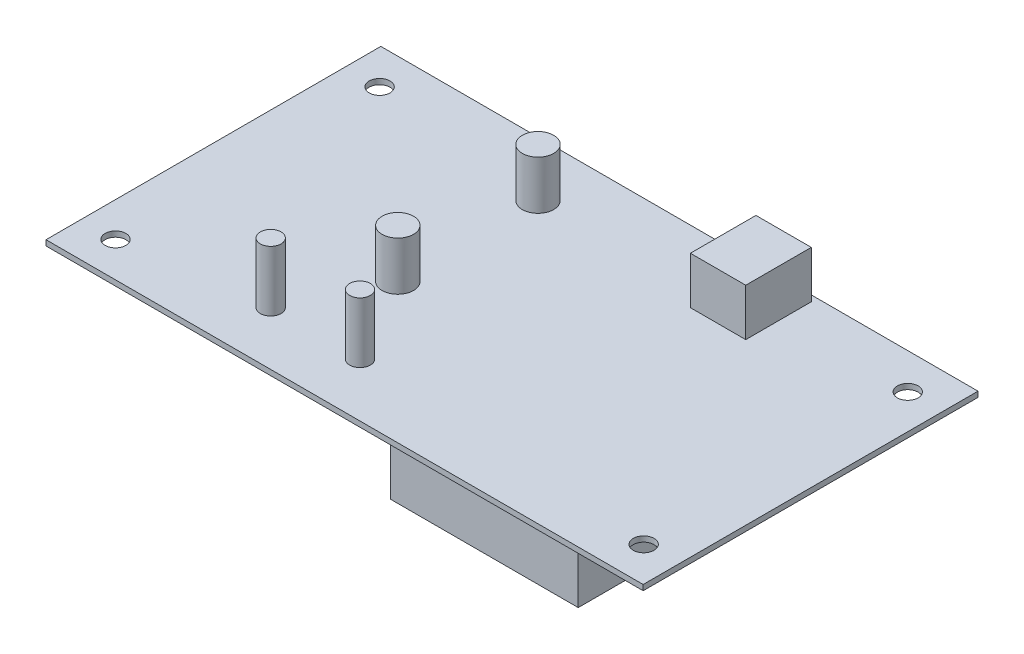
SolidWorks part; units mm, degrees
ref_plane "Front Plane" through (0, 0, 0) normal (0, 0, 1) x (1, 0, 0)
ref_plane "Top Plane" through (0, 0, 0) normal (0, 1, 0) x (1, 0, 0)
ref_plane "Right Plane" through (0, 0, 0) normal (1, 0, 0) x (0, 0, -1)
sketch "Sketch1" plane through (0, 0, 0) normal (0, 1, 0) x (1, 0, 0)
  line L1 (0, 0) -> (169.8625, 0)
  line L2 (0, 0) -> (0, 95.25)
  line L3 (0, 95.25) -> (169.8625, 95.25)
  line L4 (169.8625, 0) -> (169.8625, 95.25)
  dimension "D1" = 169.8625
  dimension "D2" = 95.25
extrude "Boss-Extrude1" add sketch "Sketch1" along normal blind 1.5494
sketch "Sketch2" plane through (0, 1.5494, 0) normal (0, 1, 0) x (1, 0, 0)
  line L0 (169.8625, 0) -> (169.8625, 95.25) construction
  line L1 (108.3945, 93.5482) -> (124.1425, 93.5482)
  line L2 (108.3945, 93.5482) -> (108.3945, 74.9046)
  line L3 (108.3945, 74.9046) -> (124.1425, 74.9046)
  line L4 (124.1425, 93.5482) -> (124.1425, 74.9046)
  line L5 (169.8625, 95.25) -> (0, 95.25) construction
  dimension "D1" = 15.748
  dimension "D2" = 18.6436
  dimension "D3" = 45.72
  dimension "D4" = 1.7018
extrude "Boss-Extrude2" add sketch "Sketch2" along normal blind 13.4112
sketch "Sketch3" plane through (0, 1.5494, 0) normal (0, 1, 0) x (1, 0, 0)
  line L0 (169.8625, 95.25) -> (0, 95.25) construction
  line L1 (0, 95.25) -> (0, 0) construction
  circle A0 centre (60.325, 79.629) radius 4.4704
  circle A1 centre (60.325, 39.751) radius 4.4704
  point P6 (0, 0)
  dimension "D1" = 8.9408
  dimension "D2" = 15.621
  dimension "D3" = 39.878
  dimension "D4" = 60.325
extrude "Boss-Extrude3" add sketch "Sketch3" along normal blind 13.843
sketch "Sketch4" plane through (0, 1.5494, 0) normal (0, 1, 0) x (1, 0, 0)
  line L0 (0, 95.25) -> (0, 0) construction
  line L1 (0, 0) -> (169.8625, 0) construction
  circle A0 centre (48.6791, 15.24) radius 2.9528
  circle A1 centre (74.0791, 15.24) radius 2.9528
  dimension "D1" = 5.9055
  dimension "D2" = 25.4
  dimension "D3" = 48.6791
  dimension "D4" = 15.24
extrude "Boss-Extrude4" add sketch "Sketch4" along normal blind 17.1704
sketch "Sketch5" plane through (0, 0, 0) normal (0, -1, 0) x (-1, 0, 0)
  line L0 (0, 0) -> (-169.8625, 0) construction
  line L1 (-96.9645, 1.0922) -> (-150.3045, 1.0922)
  line L2 (-96.9645, 1.0922) -> (-96.9645, 69.6722)
  line L3 (-96.9645, 69.6722) -> (-150.3045, 69.6722)
  line L4 (-150.3045, 1.0922) -> (-150.3045, 69.6722)
  line L5 (-169.8625, 0) -> (-169.8625, 95.25) construction
  dimension "D1" = 53.34
  dimension "D2" = 68.58
  dimension "D3" = 1.0922
  dimension "D4" = 19.558
extrude "Boss-Extrude5" add sketch "Sketch5" along normal blind 14.478
sketch "Sketch6" plane through (0, 1.5494, 0) normal (0, 1, 0) x (1, 0, 0)
  line L0 (169.8625, 95.25) -> (0, 95.25) construction
  line L2 (0, 95.25) -> (0, 0) construction
  line L5 (169.8625, 0) -> (169.8625, 95.25) construction
  line L6 (0, 0) -> (169.8625, 0) construction
  circle A0 centre (9.8108, 85.0836) radius 2.9528
  circle A1 centre (160.0517, 85.0836) radius 2.9528
  circle A2 centre (160.0517, 9.9632) radius 2.9528
  circle A3 centre (9.8108, 9.9632) radius 2.9528
  point P9 (9.8107, 88.0364)
  point P11 (6.858, 85.0836)
  point P14 (163.0045, 85.0836)
  point P18 (160.0517, 7.0104)
  point P19 (160.0517, 88.0364)
  dimension "D1" = 5.9055
  dimension "D2" = 7.2136
  dimension "D3" = 6.858
  dimension "D4" = 6.858
  dimension "D5" = 7.0104
extrude "Cut-Extrude1" cut sketch "Sketch6" against normal blind 14.478
